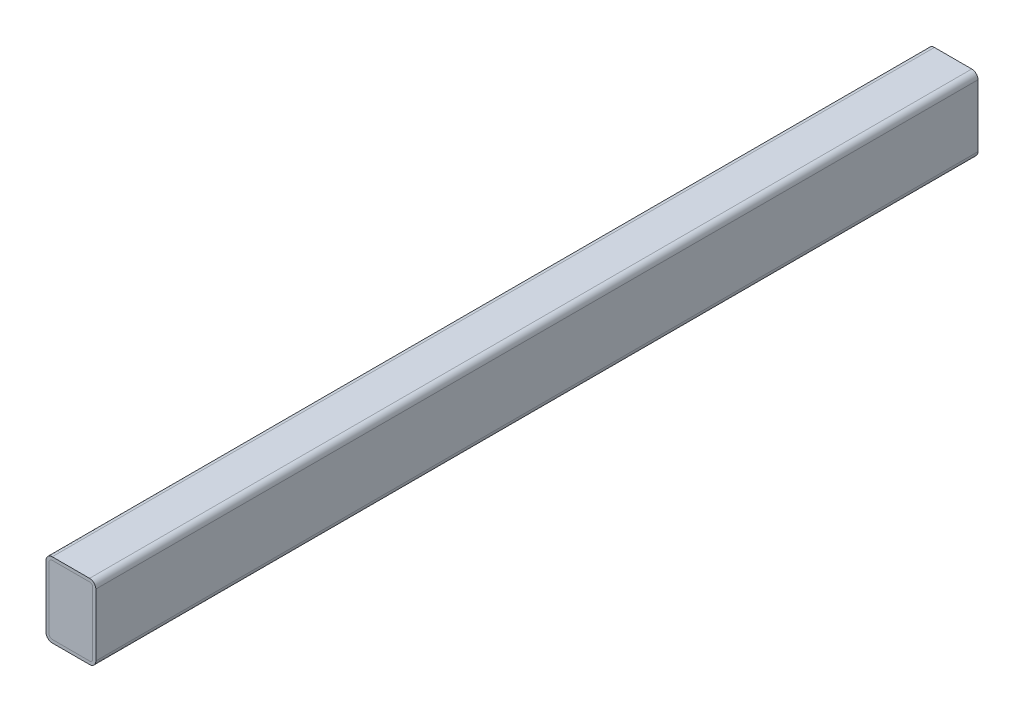
SolidWorks part; units mm, degrees
material "Plain Carbon Steel"
ref_plane "Front Plane" through (0, 0, 0) normal (0, 0, 1) x (1, 0, 0)
ref_plane "Top Plane" through (0, 0, 0) normal (0, 1, 0) x (1, 0, 0)
ref_plane "Right Plane" through (0, 0, 0) normal (1, 0, 0) x (0, 0, -1)
sketch "Sketch13" plane through (0, 0, 0) normal (0, 0, 1) x (1, 0, 0)
  line L4 (19.05, -38.1) -> (-19.05, -38.1)
  line L5 (25.4, 31.75) -> (25.4, -31.75)
  line L6 (-25.4, -31.75) -> (-25.4, 31.75)
  line L7 (-19.05, 38.1) -> (19.05, 38.1)
  line L8 (19.05, -34.925) -> (-19.05, -34.925)
  line L9 (22.225, 31.75) -> (22.225, -31.75)
  line L10 (-19.05, 34.925) -> (19.05, 34.925)
  line L11 (-22.225, -31.75) -> (-22.225, 31.75)
  line L12 (-19.05, 31.75) -> (19.05, -31.75) construction
  line L13 (19.05, 31.75) -> (-19.05, -31.75) construction
  arc A4 (-25.4, -31.75) -> (-19.05, -38.1) centre (-19.05, -31.75) ccw
  arc A5 (19.05, -38.1) -> (25.4, -31.75) centre (19.05, -31.75) ccw
  arc A6 (25.4, 31.75) -> (19.05, 38.1) centre (19.05, 31.75) ccw
  arc A7 (-19.05, 38.1) -> (-25.4, 31.75) centre (-19.05, 31.75) ccw
  arc A8 (-22.225, -31.75) -> (-19.05, -34.925) centre (-19.05, -31.75) ccw
  arc A9 (19.05, -34.925) -> (22.225, -31.75) centre (19.05, -31.75) ccw
  arc A10 (22.225, 31.75) -> (19.05, 34.925) centre (19.05, 31.75) ccw
  arc A11 (-19.05, 34.925) -> (-22.225, 31.75) centre (-19.05, 31.75) ccw
  dimension "D4" = 6.35
  dimension "D2" = 50.8
  dimension "D3" = 76.2
  dimension "D1" = 3.175
extrude "Boss-Extrude2" add sketch "Sketch13" along normal mid plane 899.922 separate body
sketch "Sketch14" plane through (0, 0, 449.961) normal (0, 0, 1) x (1, 0, 0)
  line L0 (-19.05, -34.925) -> (19.05, -34.925) construction
  line L1 (22.225, -31.75) -> (22.225, 31.75) construction
  line L2 (-22.225, 31.75) -> (-22.225, -31.75) construction
  line L3 (19.05, 34.925) -> (-19.05, 34.925) construction
  line L4 (-19.05, -34.925) -> (19.05, -34.925)
  line L5 (22.225, -31.75) -> (22.225, 31.75)
  line L6 (-22.225, 31.75) -> (-22.225, -31.75)
  line L7 (19.05, 34.925) -> (-19.05, 34.925)
  arc A0 (-22.225, -31.75) -> (-19.05, -34.925) centre (-19.05, -31.75) ccw construction
  arc A1 (19.05, -34.925) -> (22.225, -31.75) centre (19.05, -31.75) ccw construction
  arc A2 (22.225, 31.75) -> (19.05, 34.925) centre (19.05, 31.75) ccw construction
  arc A3 (-19.05, 34.925) -> (-22.225, 31.75) centre (-19.05, 31.75) ccw construction
  arc A4 (-22.225, -31.75) -> (-19.05, -34.925) centre (-19.05, -31.75) ccw
  arc A5 (19.05, -34.925) -> (22.225, -31.75) centre (19.05, -31.75) ccw
  arc A6 (22.225, 31.75) -> (19.05, 34.925) centre (19.05, 31.75) ccw
  arc A7 (-19.05, 34.925) -> (-22.225, 31.75) centre (-19.05, 31.75) ccw
extrude "Boss-Extrude3" add sketch "Sketch14" against normal up to surface (899.922 mm away) separate body up to face at (0, 0, -449.961)
equation "\"M5_tap\"=4.2mm\t\t\t\t\t\t\t' Below you can do mesurements as follows: cm, mm, ft, in, m, "
equation "\"M5_clearence\"=5.5mm"
equation "\"M6_tap\"=5mm"
equation "\"M6_clearence\"=6.6mm"
